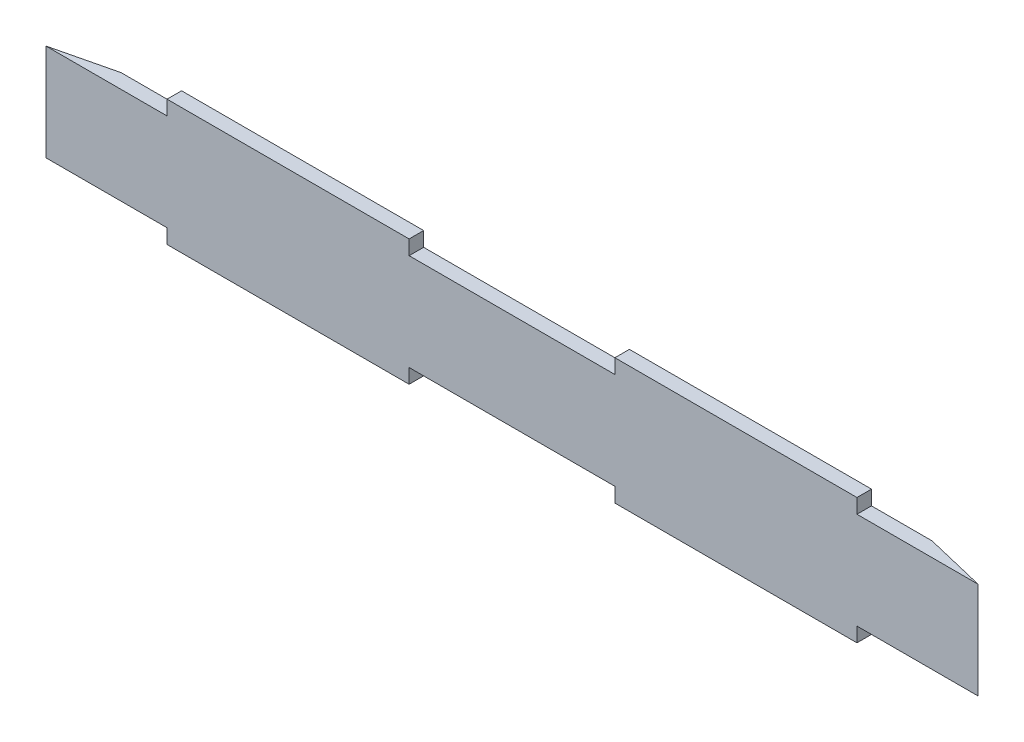
SolidWorks part; units mm, degrees
ref_plane "Plan de face" through (0, 0, 0) normal (0, 0, 1) x (1, 0, 0)
ref_plane "Plan de dessus" through (0, 0, 0) normal (0, 1, 0) x (1, 0, 0)
ref_plane "Plan de droite" through (0, 0, 0) normal (1, 0, 0) x (0, 0, -1)
sketch "Esquisse1" plane through (0, 0, 0) normal (0, 0, 1) x (1, 0, 0)
  line L1 (192.5, 20) -> (-192.5, 20)
  line L2 (192.5, 20) -> (192.5, -20)
  line L3 (192.5, -20) -> (-192.5, -20)
  line L4 (-192.5, 20) -> (-192.5, -20)
  line L5 (192.5, 20) -> (-192.5, -20) construction
  line L6 (192.5, -20) -> (-192.5, 20) construction
  point P0 (0, 0)
  dimension "D1" = 385
  dimension "D2" = 40
extrude "Boss.-Extru.1" add sketch "Esquisse1" along normal blind 6
sketch "Esquisse3" plane through (0, 0, 6) normal (0, 0, 1) x (1, 0, 0)
  line L0 (192.5, 20) -> (-192.5, 20) construction
  line L1 (-142.5, 20) -> (-42.5, 20)
  line L2 (-142.5, 20) -> (-142.5, 26)
  line L3 (-142.5, 26) -> (-42.5, 26)
  line L4 (-42.5, 20) -> (-42.5, 26)
  line L5 (-192.5, 20) -> (-192.5, -20) construction
  line L6 (42.5, 20) -> (142.5, 20)
  line L7 (42.5, 20) -> (42.5, 26)
  line L8 (42.5, 26) -> (142.5, 26)
  line L9 (142.5, 20) -> (142.5, 26)
  line L10 (-192.5, 0) -> (192.5, 0) construction
  line L11 (192.5, -20) -> (192.5, 20) construction
  line L12 (42.5, -26) -> (142.5, -26)
  line L13 (142.5, -20) -> (142.5, -26)
  line L14 (42.5, -20) -> (142.5, -20)
  line L15 (42.5, -20) -> (42.5, -26)
  line L16 (-142.5, -26) -> (-42.5, -26)
  line L17 (-42.5, -20) -> (-42.5, -26)
  line L18 (-142.5, -20) -> (-42.5, -20)
  line L19 (-142.5, -20) -> (-142.5, -26)
  dimension "D1" = 6
  dimension "D2" = 100
  dimension "D3" = 100
  dimension "D4" = 6
  dimension "D5" = 50
  dimension "D6" = 50
extrude "Boss.-Extru.2" add sketch "Esquisse3" against normal blind 6
sketch "Esquisse4" plane through (0, 20, 0) normal (0, 1, 0) x (1, 0, 0)
  line L0 (-192.5, -6) -> (-167.5, 0)
  line L1 (-142.5, 0) -> (-192.5, 0) construction
  line L2 (-167.5, 0) -> (-192.5, 0)
  line L3 (-192.5, 0) -> (-192.5, -6)
  line L4 (192.5, -6) -> (167.5, 0)
  line L5 (192.5, 0) -> (142.5, 0) construction
  line L6 (167.5, 0) -> (192.5, 0)
  line L7 (192.5, 0) -> (192.5, -6)
extrude "Enlèv. mat.-Extru.1" cut sketch "Esquisse4" against normal through all
